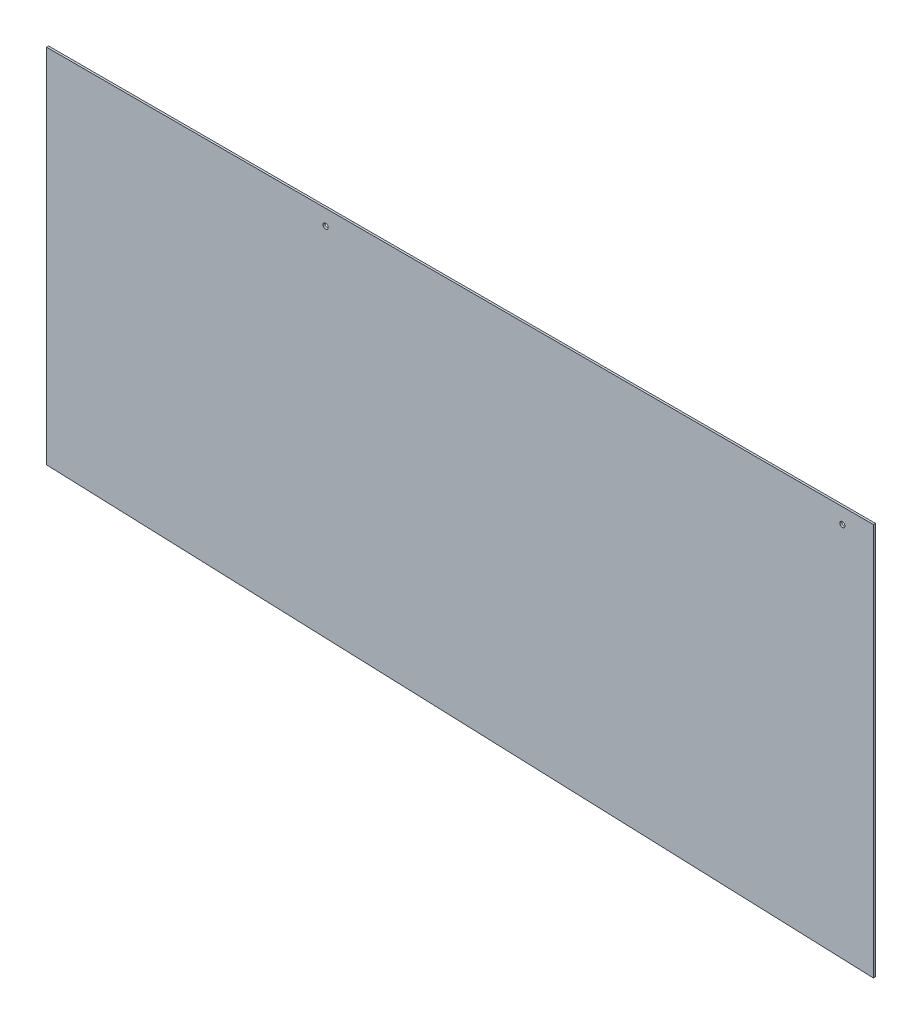
SolidWorks part; units mm, degrees
ref_plane "Ön Düzlem" through (0, 0, 0) normal (0, 0, 1) x (1, 0, 0)
ref_plane "Üst Düzlem" through (0, 0, 0) normal (0, 1, 0) x (1, 0, 0)
ref_plane "Sağ Düzlem" through (0, 0, 0) normal (1, 0, 0) x (0, 0, -1)
sketch "Sketch1" plane through (0, 0, 0) normal (0, 0, 1) x (1, 0, 0)
  line L0 (-31.8126, 14.0444) -> (48.1874, 14.0444)
  line L1 (48.1874, 14.0444) -> (48.1874, -20.9556)
  line L2 (48.1874, -20.9556) -> (-31.8126, -20.9556)
  line L3 (-31.8126, -20.9556) -> (-31.8126, 14.0444)
  circle A0 centre (-4.8126, 12.5444) radius 0.25
  circle A1 centre (45.1874, 12.5444) radius 0.25
  dimension "D4" = 1.5
  dimension "D6" = 50
  dimension "D1" = 80
  dimension "D2" = 35
  dimension "D3" = 35
  dimension "D5" = 3
extrude "Boss-Extrude4" add sketch "Sketch1" along normal blind 0.2
sketch "Sketch3" plane through (0, 0, 0.2) normal (0, 0, 1) x (1, 0, 0)
  line L0 (-31.8126, -20.9556) -> (48.1874, -23.9556)
  line L1 (48.1874, -23.9556) -> (48.1874, -20.9556)
  line L6 (-31.8126, 14.0444) -> (-31.8126, -20.9556)
  line L7 (-31.8126, -20.9556) -> (48.1874, -20.9556)
  line L8 (48.1874, -20.9556) -> (48.1874, 14.0444)
  line L9 (48.1874, 14.0444) -> (-31.8126, 14.0444)
  line L11 (-31.8126, -20.9556) -> (48.1874, -20.9556)
  dimension "D1" = 3
  dimension "D2" = 80
  dimension "D3" = 0
extrude "Boss-Extrude5" add sketch "Sketch3" against normal blind 0.2
